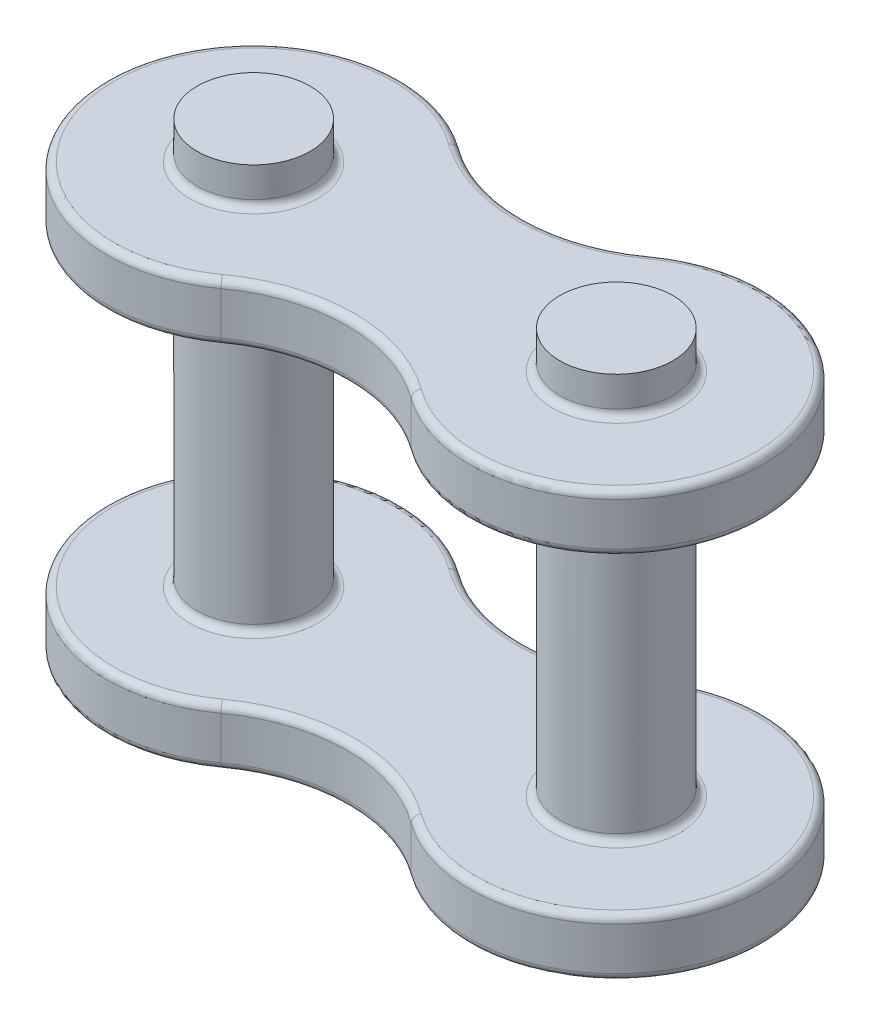
SolidWorks part; units mm, degrees
material "Alloy Steel"
ref_plane "X-Y Datum" through (0, 0, 0) normal (0, 0, 1) x (1, 0, 0)
ref_plane "X-Z Datum" through (0, 0, 0) normal (0, 1, 0) x (1, 0, 0)
ref_plane "Y-Z Datum" through (0, 0, 0) normal (1, 0, 0) x (0, 0, -1)
sketch "Sketch2" plane through (0, 0, 0) normal (0, 1, 0) x (1, 0, 0)
  line L0 (0, -9.7123) -> (0, 9.7123) construction
  line L1 (12.7033, 0) -> (-12.7033, 0) construction
  circle A0 centre (-6.35, 0) radius 1.98
  arc A1 (-3.3293, 4.163) -> (-3.3293, -4.163) centre (-6.35, 0) ccw
  circle A2 centre (6.35, 0) radius 1.98
  arc A3 (3.3293, 4.163) -> (3.3293, -4.163) centre (6.35, 0) cw
  arc A4 (-3.3293, 4.163) -> (3.3293, 4.163) centre (0, 8.7513) ccw
  arc A5 (-3.3293, -4.163) -> (3.3293, -4.163) centre (0, -8.7513) cw
  point P4 (0, 0)
  point P8 (0, 0)
  dimension "D1" = 10.287
  dimension "D2" = 3.96
  dimension "D3" = 6.35
extrude "Boss-Extrude1" add sketch "Sketch2" along normal mid plane 2.0066
ref_plane "Center Plane" through (0, 6.4389, 0) normal (0, 1, 0) x (1, 0, 0)
sketch "Sketch5" plane through (0, 6.4389, 0) normal (0, 1, 0) x (1, 0, 0)
  line L0 (0, -55) -> (0, 55) construction
  circle A0 centre (-6.35, 0) radius 1.98 construction
  circle A1 centre (-6.35, 0) radius 1.98
  circle A2 centre (6.35, 0) radius 1.98
extrude "Boss-Extrude2" add sketch "Sketch5" along normal mid plane 17.5006
fillet "Fillet1" radius 0.254 12 edges at (11.4935, -1.0033, 0) (0, -1.0033, 3.0824) (-11.4935, -1.0033, 0) (0, 1.0033, -3.0824) (11.4935, 1.0033, 0) (0, 1.0033, 3.0824) (-6.35, -1.0033, 1.98) (6.35, -1.0033, 1.98) (6.35, 1.0033, -1.98) (-6.35, 1.0033, 1.98) (0, -1.0033, -3.0824) (-11.4935, 1.0033, 0)
mirror "Mirror1" about plane through (0, 6.4389, 0) normal (0, 1, 0) of "Fillet1", "Boss-Extrude1"
ref_plane "Plane1" through (0, 6.4389, 0) normal (0, 1, 0) x (1, 0, 0)
